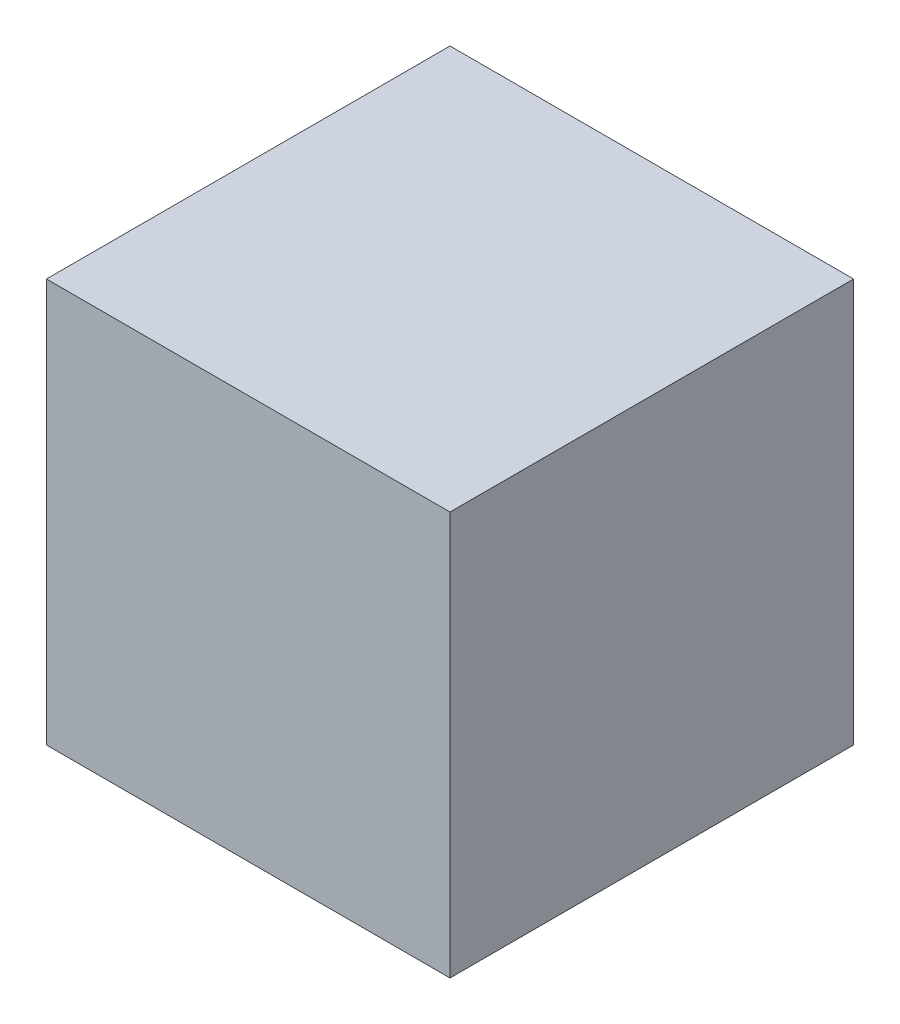
SolidWorks part; units mm, degrees
material "Cedar"
ref_plane "Front Plane" through (0, 0, 0) normal (0, 0, 1) x (1, 0, 0)
ref_plane "Top Plane" through (0, 0, 0) normal (0, 1, 0) x (1, 0, 0)
ref_plane "Right Plane" through (0, 0, 0) normal (1, 0, 0) x (0, 0, -1)
sketch "Sketch1" plane through (0, 0, 0) normal (0, 1, 0) x (1, 0, 0)
  line L1 (-13.8906, -13.8906) -> (13.8906, -13.8906)
  line L2 (-13.8906, -13.8906) -> (-13.8906, 13.8906)
  line L3 (-13.8906, 13.8906) -> (13.8906, 13.8906)
  line L4 (13.8906, -13.8906) -> (13.8906, 13.8906)
  line L5 (-13.8906, -13.8906) -> (13.8906, 13.8906) construction
  line L6 (-13.8906, 13.8906) -> (13.8906, -13.8906) construction
  point P0 (0, 0)
  dimension "D1" = 27.7812
  dimension "D2" = 27.7812
extrude "Boss-Extrude1" add sketch "Sketch1" along normal blind 27.7812
